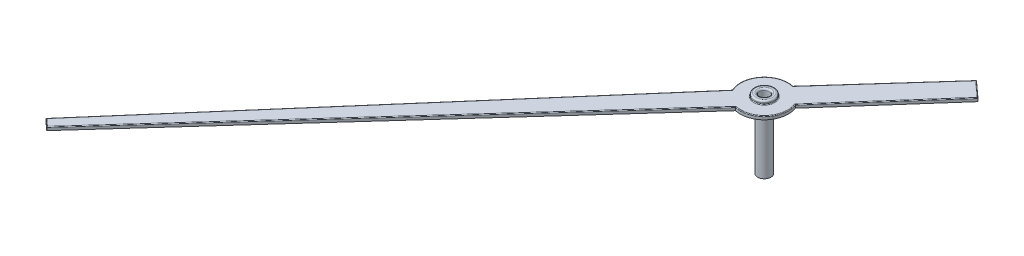
SolidWorks part; units mm, degrees
ref_plane "Front Plane" through (0, 0, 0) normal (0, 0, 1) x (1, 0, 0)
ref_plane "Top Plane" through (0, 0, 0) normal (0, 1, 0) x (1, 0, 0)
ref_plane "Right Plane" through (0, 0, 0) normal (1, 0, 0) x (0, 0, -1)
sketch "Sketch1" plane through (0, 0, 0) normal (0, 1, 0) x (1, 0, 0)
  line L0 (-82.6439, -49.511) -> (-82.4063, -49.7259)
  line L1 (-82.4063, -49.7259) -> (-72.593, -38.8754)
  line L2 (-82.6439, -49.511) -> (-73.0842, -38.4816)
  line L3 (-69.6713, -34.5695) -> (-69.1911, -35.004)
  line L4 (-72.2753, -37.4696) -> (-69.6713, -34.5695)
  line L5 (-69.1911, -35.004) -> (-71.7603, -37.9148)
  line L6 (-69.1911, -35.004) -> (-69.1864, -35.0126)
  arc A0 (-72.2753, -37.4696) -> (-73.0842, -38.4816) centre (-72.4331, -38.1727) ccw
  arc A1 (-72.593, -38.8754) -> (-71.7603, -37.9148) centre (-72.4331, -38.1727) ccw
  circle A2 centre (-72.4331, -38.1727) radius 0.15
  dimension "D1" = 0.3
extrude "Boss-Extrude1" add sketch "Sketch1" along normal blind 0.1 contours L1 A1 L5 L3 L4 A0 L2 L0 A2
sketch "Sketch2" plane through (0, 0.1, 0) normal (0, 1, 0) x (1, 0, 0)
  circle A0 centre (-72.4331, -38.1727) radius 0.3
  circle A1 centre (-72.4331, -38.1727) radius 0.15
  dimension "D1" = 0.6
  dimension "D2" = 0.3
extrude "Boss-Extrude2" add sketch "Sketch2" along normal blind 0.1 and the other way blind 2
fillet "Fillet1" radius 0.05 2 edges at (-72.4331, 0.2, 38.3227) (-72.4331, 0.2, 38.4727)
fillet "Fillet2" radius 0.02 9 edges at (-82.5251, 0.1, 49.6184) (-77.864, 0.1, 43.9963) (-72.996, 0.1, 37.7228) (-70.9733, 0.1, 36.0195) (-69.4312, 0.1, 34.7867) (-70.4757, 0.1, 36.4594) (-71.8886, 0.1, 38.6447) (-77.4996, 0.1, 44.3006) (-72.4331, 0.1, 38.4727)
sketch "Sketch3" plane through (0, -1.9, 0) normal (0, -1, 0) x (1, 0, 0)
  circle A0 centre (-72.4331, 38.1727) radius 0.2
  circle A1 centre (-72.4331, 38.1727) radius 0.4314
  dimension "D1" = 0.4
extrude "Cut-Extrude1" cut sketch "Sketch3" against normal up to surface (1.9 mm away) up to face at (-72.4331, 0, 38.4727)
